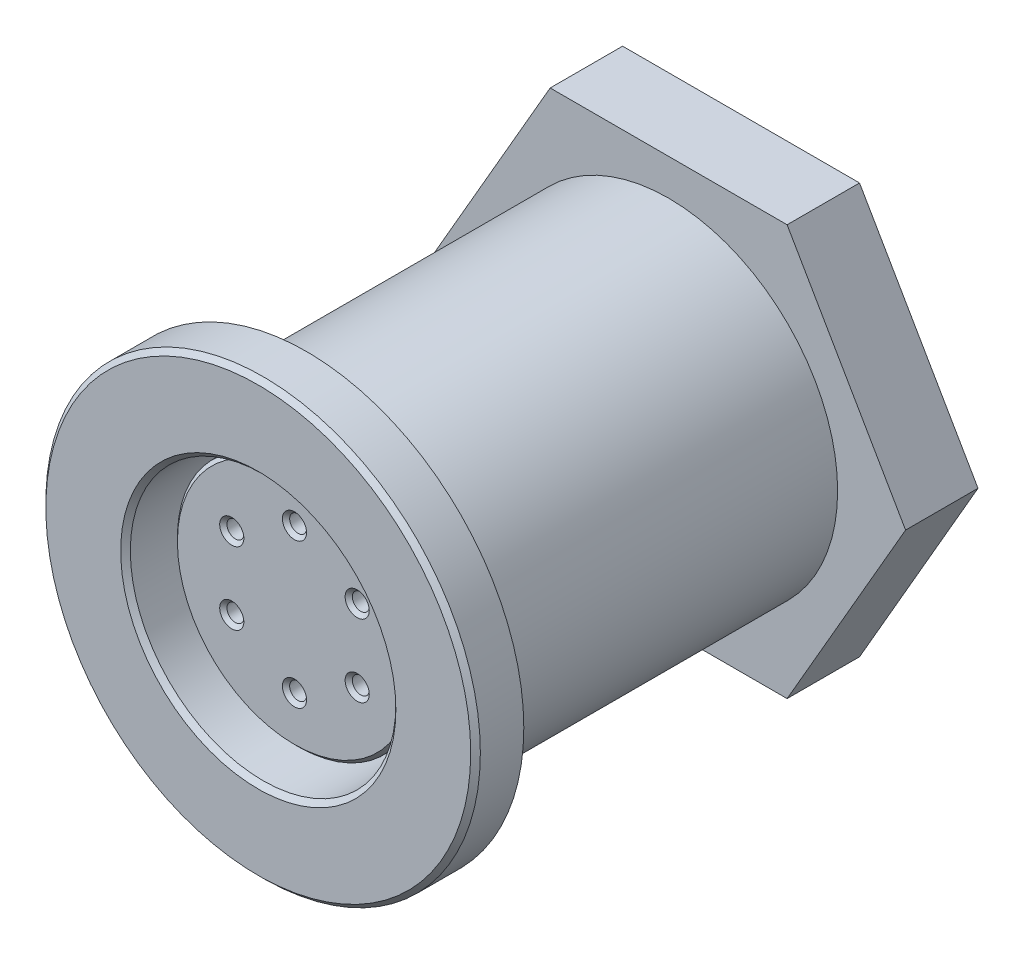
SolidWorks part; units mm, degrees
material "1060 Alloy"
ref_plane "Front Plane" through (0, 0, 0) normal (0, 0, 1) x (1, 0, 0)
ref_plane "Top Plane" through (0, 0, 0) normal (0, 1, 0) x (1, 0, 0)
ref_plane "Right Plane" through (0, 0, 0) normal (1, 0, 0) x (0, 0, -1)
sketch "Sketch1" plane through (0, 0, 0) normal (0, 0, 1) x (1, 0, 0)
  circle A0 centre (0, 0) radius 9
extrude "Extrude1" add sketch "Sketch1" along normal blind 2
sketch "Sketch3" plane through (0, 0, 0) normal (0, 0, -1) x (-1, 0, 0)
  circle A0 centre (0, 0) radius 7.8
  circle A1 centre (0, 0) radius 7
sketch "Sketch4" plane through (0, 0, 0) normal (0, 0, -1) x (-1, 0, 0)
  circle A0 centre (0, 0) radius 7
extrude "Extrude2" add sketch "Sketch4" along normal blind 19
sketch "Sketch2" plane through (0, 0, 2) normal (0, 0, 1) x (1, 0, 0)
  circle A0 centre (0, 0) radius 5.5
extrude "Cut-Extrude1" cut sketch "Sketch2" against normal blind 10
extrude "Cut-Extrude2" cut sketch "Sketch3" against normal blind 1
sketch "Sketch5" plane through (0, 0, -8) normal (0, 0, 1) x (1, 0, 0)
  circle A0 centre (0, 0) radius 5
extrude "Extrude3" add sketch "Sketch5" along normal blind 8.5
sketch "Sketch6" plane through (0, 0, 0.5) normal (0, 0, 1) x (1, 0, 0)
  circle A0 centre (0, 3) radius 0.35
  circle A1 centre (0, -3) radius 0.35
  circle A2 centre (2.5981, 1.5) radius 0.35
  circle A3 centre (2.5981, -1.5) radius 0.35
  circle A4 centre (-2.5981, 1.5) radius 0.35
  circle A5 centre (-2.5981, -1.5) radius 0.35
  dimension "D1" = 3
  dimension "D3" = 3
  dimension "D2" = 3
  dimension "D4" = 3
  dimension "D5" = 3
  dimension "D6" = 3
  dimension "D7" = 3
  dimension "D8" = 3
extrude "Cut-Extrude3" cut sketch "Sketch6" against normal blind 7
chamfer "Chamfer2" distance 0.15 angle 45 7 edges at (5, 0, 0.5) (0.35, -3, 0.5) (0.35, 3, 0.5) (2.9481, -1.5, 0.5) (2.9481, 1.5, 0.5) (-2.2481, -1.5, 0.5) (-2.2481, 1.5, 0.5)
chamfer "Chamfer1" distance 0.2 angle 45 2 edges at (9, 0, 2) (5.5, 0, 2)
sketch "Sketch7" plane through (0, 0, -19) normal (0, 0, -1) x (-1, 0, 0)
  circle A0 centre (0, 0) radius 5
extrude "Cut-Extrude4" cut sketch "Sketch7" against normal blind 1
chamfer "Chamfer3" distance 0.5 angle 45 1 edges at (-7, 0, -19)
sketch "Sketch8" plane through (0, 0, -18) normal (0, 0, -1) x (-1, 0, 0)
  line L0 (-4.9075, 8.5) -> (4.9075, 8.5)
  line L1 (4.9075, 8.5) -> (9.815, 0)
  line L2 (9.815, 0) -> (4.9075, -8.5)
  line L3 (4.9075, -8.5) -> (-4.9075, -8.5)
  line L4 (-4.9075, -8.5) -> (-9.815, 0)
  line L5 (-9.815, 0) -> (-4.9075, 8.5)
  line L6 (0, 8.5) -> (0, -8.5) construction
  dimension "D1" = 17
  dimension "D2" = 17
extrude "Extrude4" add sketch "Sketch8" against normal blind 3
